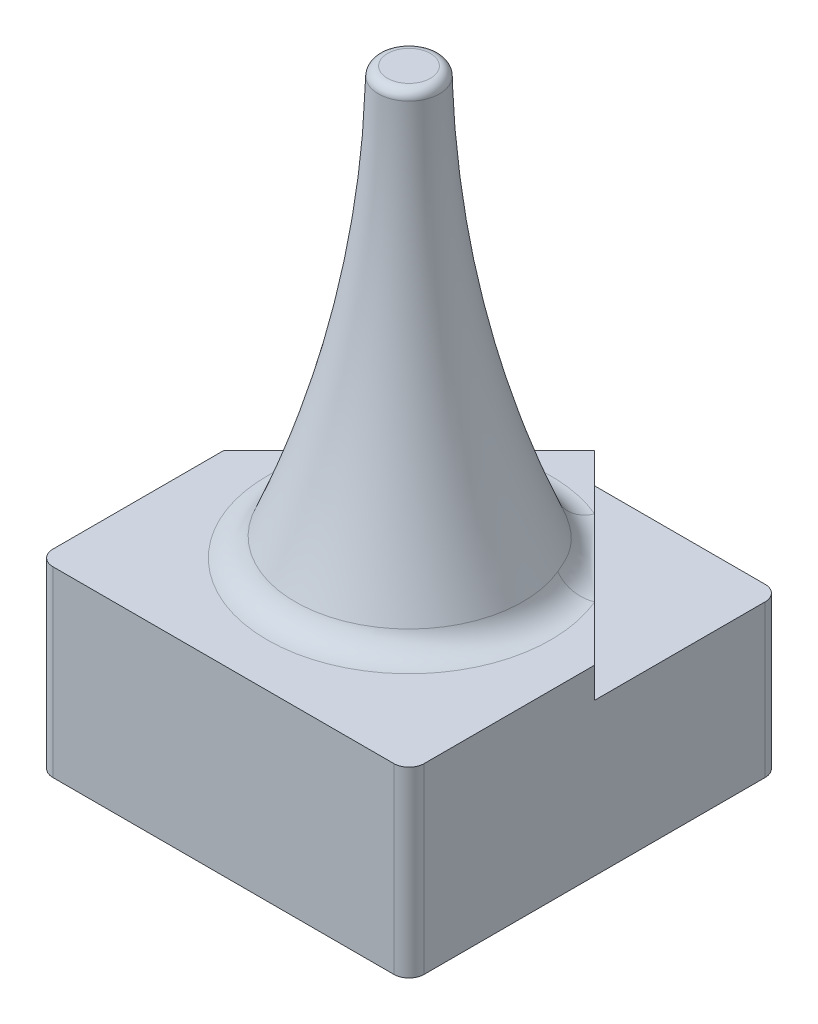
SolidWorks part; units mm, degrees
ref_plane "Plan de face" through (0, 0, 0) normal (0, 0, 1) x (1, 0, 0)
ref_plane "Plan de dessus" through (0, 0, 0) normal (0, 1, 0) x (1, 0, 0)
ref_plane "Plan de droite" through (0, 0, 0) normal (1, 0, 0) x (0, 0, -1)
sketch "Esquisse1" plane through (0, 0, 0) normal (0, 1, 0) x (1, 0, 0)
  line L1 (-6.1, -6.1) -> (6.1, -6.1)
  line L2 (-6.1, -6.1) -> (-6.1, 6.1)
  line L3 (-6.1, 6.1) -> (6.1, 6.1)
  line L4 (6.1, -6.1) -> (6.1, 6.1)
  line L5 (-6.1, -6.1) -> (6.1, 6.1) construction
  line L6 (-6.1, 6.1) -> (6.1, -6.1) construction
  point P0 (0, 0)
  dimension "D1" = 12.2
  dimension "D2" = 12.2
extrude "Boss.-Extru.1" add sketch "Esquisse1" along normal blind 6
sketch "Esquisse2" plane through (0, 6, 0) normal (0, 1, 0) x (1, 0, 0)
  line L0 (-6.1, 0) -> (0, 6.1)
  line L1 (-6.1, 6.1) -> (-6.1, -6.1) construction
  line L2 (6.1, 6.1) -> (-6.1, 6.1) construction
  line L3 (0, 6.1) -> (6.1, 0)
  line L4 (6.1, -6.1) -> (6.1, 6.1) construction
  line L5 (6.1, 0) -> (6.1, 6.1)
  line L6 (6.1, 6.1) -> (-6.1, 6.1)
  line L7 (-6.1, 6.1) -> (-6.1, 0)
  line M1 (6.1, -6.1) -> (6.1, 6.1)
  line M2 (6.1, 6.1) -> (-6.1, 6.1)
  line M3 (-6.1, 6.1) -> (-6.1, -6.1)
extrude "Enlèv. mat.-Extru.1" cut sketch "Esquisse2" against normal blind 1 contours L0 M3 M2 | L3 M2 M1
sketch "Esquisse4" plane through (0, 0, 0) normal (0, 0, 1) x (1, 0, 0)
  line L0 (-6.1, 6) -> (6.1, 6) construction
  line L1 (0, 20) -> (0, 6)
  line L2 (0, 6) -> (4, 6)
  line L3 (1, 20) -> (0, 20)
  spline S0 degree 2 poles (4, 6) (1.1185, 12.6471) (1, 20) knots 0 0 0 1 1 1
  dimension "D1" = 4
  dimension "D2" = 14
  dimension "D3" = 1
revolve "Révolution1" add sketch "Esquisse4" angle 360 about L1
fillet "Congé2" radius 0.3 1 edges at (-1, 20, 0)
fillet "Congé3" radius 0.5 4 edges at (-6.1, 2.5, -6.1) (6.1, 2.5, -6.1) (6.1, 3, 6.1) (-6.1, 3, 6.1)
sketch "Esquisse5" plane through (0, 0, 0) normal (0, 0, 1) x (1, 0, 0)
  line L0 (6.1, 6) -> (6.1, 0) construction
  line L1 (-0.15, 17) -> (-0.15, 0)
  line L2 (-0.15, 0) -> (4.4724, 0)
  line L3 (0.7131, 17) -> (-0.15, 17)
  line L4 (-5.6, 0) -> (5.6, 0) construction
  spline S0 degree 3 poles (4.4724, 0) (2.63, 3.8311) (1.0721, 14.1151) (0.7131, 17) knots 0 0 0 0 1 1 1 1
  dimension "D2" = 17
  dimension "D4" = 0
  dimension "D6" = 6.25
revolve "Enlèvement de matière-Révolution1" cut sketch "Esquisse5" angle 360 about L1
fillet "Congé4" radius 1 1 edges at (-4, 6, 0)
